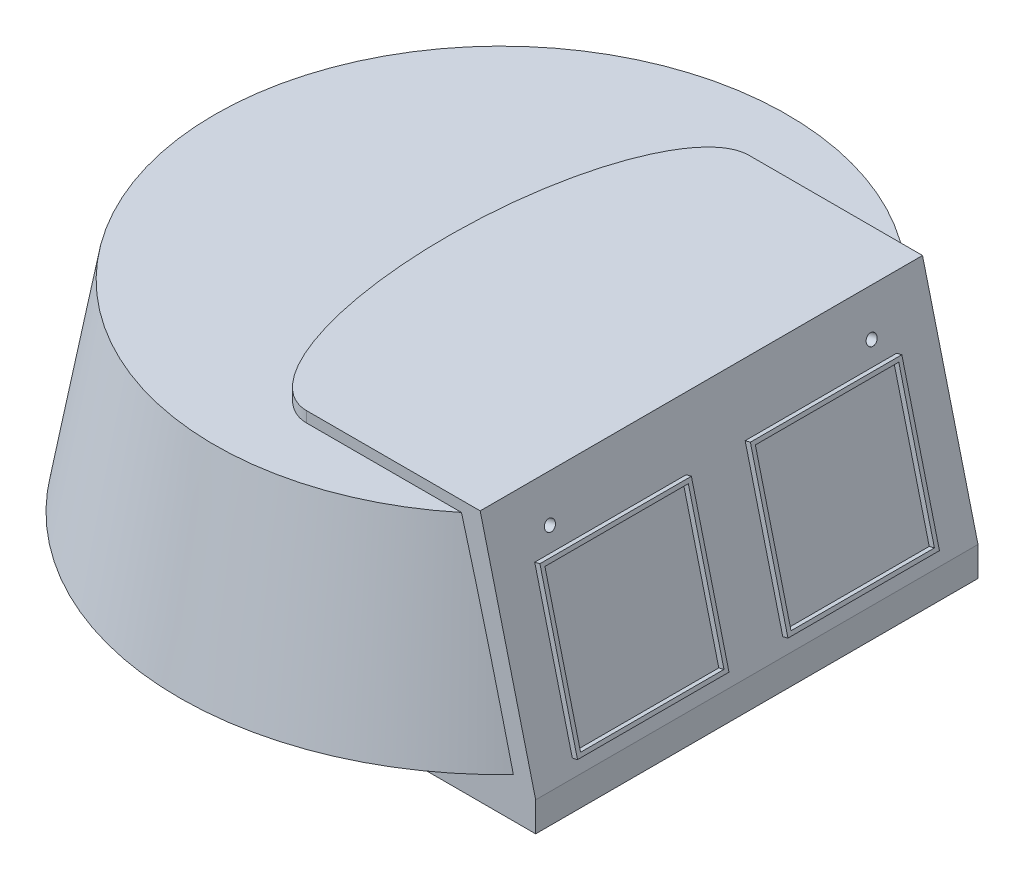
SolidWorks part; units mm, degrees
ref_plane "Front Plane" through (0, 0, 0) normal (0, 0, 1) x (1, 0, 0)
ref_plane "Top Plane" through (0, 0, 0) normal (0, 1, 0) x (1, 0, 0)
ref_plane "Right Plane" through (0, 0, 0) normal (1, 0, 0) x (0, 0, -1)
sketch "Sketch1" plane through (0, 0, 0) normal (0, 0, 1) x (1, 0, 0)
  line L0 (0, 0) -> (240, 0) construction
  line L1 (240, 0) -> (213.551, 150)
  line L2 (213.551, 150) -> (0, 150)
  line L3 (0, 150) -> (0, 0)
  line L4 (0, -30) -> (180, -30)
  line L6 (0, -30) -> (0, 0)
  line L7 (180, -30) -> (193.3569, 0)
  line L8 (193.3569, 0) -> (240, 0)
  dimension "D1" = 240
  dimension "D2" = 80
  dimension "D3" = 150
  dimension "D4" = 30
  dimension "D5" = 66
  dimension "D6" = 180
revolve "Revolve1" add sketch "Sketch1" angle 360 about L3
sketch "Sketch2" plane through (0, 0, 0) normal (0, 0, 1) x (1, 0, 0)
  line L0 (0, 150) -> (0, -30) construction
  line L1 (20, -30) -> (144.5191, -30)
  line L2 (144.5191, -30) -> (249.534, -30)
  line L3 (249.534, -30) -> (249.534, -8)
  line L4 (20, 158) -> (20, -30)
  line L5 (213.551, 150) -> (-213.551, 150) construction
  line L6 (-180, -30) -> (180, -30) construction
  line L11 (198.5521, -8) -> (249.534, -8)
  line L12 (198.5521, -8) -> (249.534, -8) construction
  line L13 (220.2637, 158) -> (-8, 158)
  line L14 (249.534, -8) -> (220.2637, 158)
  line L15 (185.1953, -38) -> (198.5521, -8)
  line L16 (-8, -38) -> (185.1953, -38)
  line L17 (-8, 0) -> (-8, -38)
  line L18 (-8, 158) -> (-8, 0)
  line L19 (220.2637, 158) -> (20, 158)
  line L20 (249.534, -8) -> (220.2637, 158)
  line L23 (188.7571, -30) -> (198.5521, -8) construction
  dimension "D2" = 20
  dimension "D1" = 8
extrude "Boss-Extrude6" add sketch "Sketch2" along normal mid plane 330
sketch "Sketch4" plane through (0, 150, 0) normal (0, 1, 0) x (1, 0, 0)
  line L2 (20, -165) -> (20, 165) construction
  line L3 (220.2637, 165) -> (20, 165) construction
  ellipse E0 centre (20, 0) end of major axis (20, 165) minor radius 60
  dimension "D1" = 60
sketch "Sketch5" plane through (0, 0, 0) normal (0, 0, 1) x (1, 0, 0)
  line L0 (0, -30) -> (0, -60)
  line L1 (-180, -30) -> (71.9375, -30) construction
  line L2 (0, -60) -> (90, -60)
  line L3 (90, -60) -> (105, -30)
  line L5 (105, -30) -> (0, -30)
  dimension "D1" = 90
  dimension "D2" = 105
  dimension "D3" = 30
revolve "Revolve3" add sketch "Sketch5" angle 360 about L0
sketch "Sketch7" plane through (0, 0, 0) normal (0, 0, 1) x (1, 0, 0)
  line L0 (149.534, 158) -> (190.9225, -8)
  line L1 (220.2637, 158) -> (20, 158) construction
  line L2 (71.9375, -30) -> (249.534, -30) construction
  line L3 (190.9225, -8) -> (190.9225, -30)
  line L7 (149.534, 158) -> (249.534, 158)
  line L8 (249.534, 158) -> (249.534, -30)
  line L9 (249.534, -30) -> (190.9225, -30)
  line L11 (249.534, -30) -> (249.534, -8) construction
  line L12 (220.2637, 158) -> (20, 158) construction
  dimension "D1" = 100
  dimension "D2" = 76
extrude "Cut-Extrude3" cut sketch "Sketch7" against normal through all both and the other way through all
shell "Shell1" thickness 10
sketch "Sketch8" plane through (177.8706, 44.3481, 0) normal (0.9703, 0.2419, 0) x (0, 0, -1)
  line L0 (-132, 70) -> (-25, 70)
  line L3 (-132, -40) -> (-132, 70)
  line L4 (-135, 73) -> (-22, 73)
  line L6 (-22, -43) -> (-135, -43)
  line L7 (-135, -43) -> (-135, 73)
  line L8 (0, 70) -> (0, -40) construction
  line L9 (-25, 70) -> (-25, -40)
  line L10 (-22, 73) -> (-22, -43)
  line L11 (-135, 73) -> (138, 73) construction
  line L12 (165, -53.9507) -> (-165, -53.9507) construction
  line L13 (-132, 70) -> (135, 70) construction
  line L14 (-25, -40) -> (-132, -40)
  line L15 (135, -40) -> (-132, -40) construction
  line L16 (138, -43) -> (-135, -43) construction
  line L17 (135, 70) -> (135, -40) construction
  line L18 (138, 73) -> (138, -43) construction
  line L19 (25, -40) -> (132, -40)
  line L20 (22, 73) -> (22, -43)
  line L21 (25, 70) -> (25, -40)
  line L22 (135, -43) -> (135, 73)
  line L23 (22, -43) -> (135, -43)
  line L24 (135, 73) -> (22, 73)
  line L25 (132, -40) -> (132, 70)
  line L26 (132, 70) -> (25, 70)
  dimension "D1" = 110
  dimension "D2" = 107
  dimension "D3" = 10.9507
  dimension "D5" = 22
  dimension "D6" = 3
  dimension "D4" = 3
extrude "Boss-Extrude5" add sketch "Sketch8" along normal blind 4
extrude "Boss-Extrude7" add sketch "Sketch4" along normal up to surface (8 mm away) contours E0 up to face at (84.767, 158, 0)
sketch "Sketch9" plane through (177.8706, 44.3481, 0) normal (0.9703, 0.2419, 0) x (0, 0, -1)
  line L0 (-22, 73) -> (-135, 73) construction
  circle A0 centre (-120, 88) radius 4
  dimension "D1" = 8
  dimension "D2" = 120
  dimension "D3" = 15
extrude "Cut-Extrude4" cut sketch "Sketch9" against normal blind 10
mirror "Mirror1" about plane through (0, 0, 0) normal (0, 0, 1) of "Cut-Extrude4"
scale "Scale1" scale about origin uniform scaling yes scale factor 0.5
